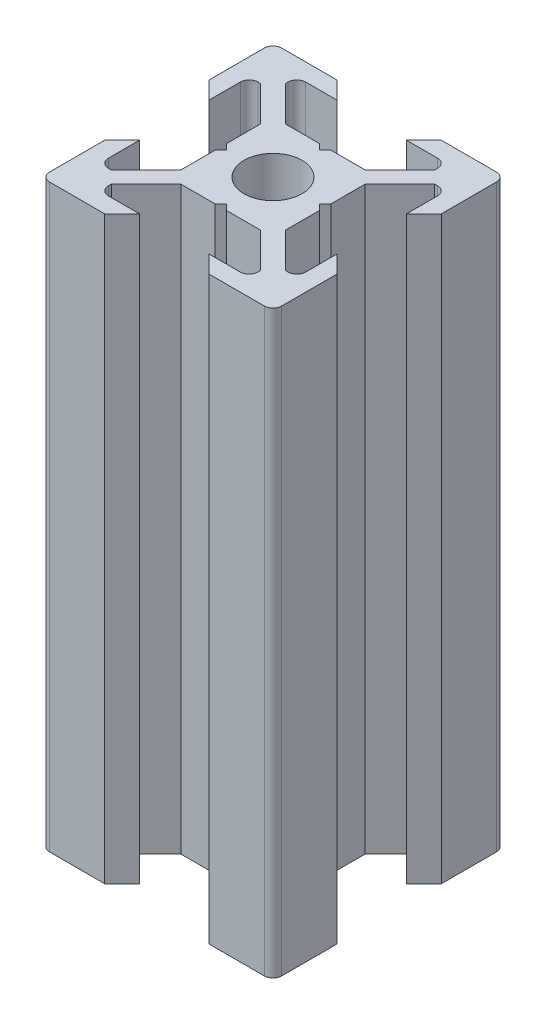
SolidWorks part; units mm, degrees
ref_plane "Face" through (0, 0, 0) normal (0, 0, 1) x (1, 0, 0)
ref_plane "Dessus" through (0, 0, 0) normal (0, 1, 0) x (1, 0, 0)
ref_plane "Droite" through (0, 0, 0) normal (1, 0, 0) x (0, 0, -1)
sketch "Esquisse1" plane through (0, 0, 0) normal (0, 1, 0) x (1, 0, 0)
  line L0 (0, 0) -> (0, 10) construction
  line L1 (0, 0) -> (-10, 0) construction
  line L2 (-10, 0) -> (-10, 10) construction
  line L3 (-10, 10) -> (0, 10) construction
  line L4 (0, 4) -> (-0.5, 4.5)
  line L5 (-0.5, 4.5) -> (-3.4393, 4.5)
  line L6 (-3.4393, 4.5) -> (-6.4393, 7.5)
  line L7 (-6.4393, 7.5) -> (-6.4393, 8.5)
  line L8 (-6.4393, 8.5) -> (-3, 8.5)
  line L9 (-3, 8.5) -> (-4.5, 10)
  line L10 (-4.5, 10) -> (-10, 10)
  line L11 (0, 0) -> (-10, 10) construction
  line L12 (-10, 4.5) -> (-10, 10)
  line L13 (-8.5, 3) -> (-10, 4.5)
  line L14 (-8.5, 6.4393) -> (-8.5, 3)
  line L15 (-7.5, 6.4393) -> (-8.5, 6.4393)
  line L16 (-4.5, 3.4393) -> (-7.5, 6.4393)
  line L17 (-4.5, 0.5) -> (-4.5, 3.4393)
  line L18 (-4, 0) -> (-4.5, 0.5)
  line L19 (0, -4) -> (-0.5, -4.5)
  line L20 (-0.5, -4.5) -> (-3.4393, -4.5)
  line L21 (-4, 0) -> (-4.5, -0.5)
  line L22 (-4.5, -0.5) -> (-4.5, -3.4393)
  line L23 (-4.5, -3.4393) -> (-7.5, -6.4393)
  line L24 (-3.4393, -4.5) -> (-6.4393, -7.5)
  line L25 (-3, -8.5) -> (-4.5, -10)
  line L26 (-6.4393, -8.5) -> (-3, -8.5)
  line L27 (-6.4393, -7.5) -> (-6.4393, -8.5)
  line L28 (-7.5, -6.4393) -> (-8.5, -6.4393)
  line L29 (-4.5, -10) -> (-10, -10)
  line L30 (-10, -4.5) -> (-10, -10)
  line L31 (-8.5, -3) -> (-10, -4.5)
  line L32 (-8.5, -6.4393) -> (-8.5, -3)
  line L33 (8.5, -6.4393) -> (8.5, -3)
  line L34 (8.5, -3) -> (10, -4.5)
  line L35 (10, -4.5) -> (10, -10)
  line L36 (4.5, -10) -> (10, -10)
  line L37 (7.5, -6.4393) -> (8.5, -6.4393)
  line L38 (6.4393, -7.5) -> (6.4393, -8.5)
  line L39 (6.4393, -8.5) -> (3, -8.5)
  line L40 (3, -8.5) -> (4.5, -10)
  line L41 (3.4393, -4.5) -> (6.4393, -7.5)
  line L42 (4.5, -3.4393) -> (7.5, -6.4393)
  line L43 (4.5, -0.5) -> (4.5, -3.4393)
  line L44 (4, 0) -> (4.5, -0.5)
  line L45 (0.5, -4.5) -> (3.4393, -4.5)
  line L46 (0, -4) -> (0.5, -4.5)
  line L47 (4, 0) -> (4.5, 0.5)
  line L48 (4.5, 0.5) -> (4.5, 3.4393)
  line L49 (4.5, 3.4393) -> (7.5, 6.4393)
  line L50 (7.5, 6.4393) -> (8.5, 6.4393)
  line L51 (8.5, 6.4393) -> (8.5, 3)
  line L52 (8.5, 3) -> (10, 4.5)
  line L53 (10, 4.5) -> (10, 10)
  line L54 (4.5, 10) -> (10, 10)
  line L55 (3, 8.5) -> (4.5, 10)
  line L56 (6.4393, 8.5) -> (3, 8.5)
  line L57 (6.4393, 7.5) -> (6.4393, 8.5)
  line L58 (3.4393, 4.5) -> (6.4393, 7.5)
  line L59 (0.5, 4.5) -> (3.4393, 4.5)
  line L60 (0, 4) -> (0.5, 4.5)
  circle A0 centre (0, 0) radius 2.5
  dimension "D10" = 5
  dimension "D1" = 10
  dimension "D2" = 45
  dimension "D3" = 45
  dimension "D4" = 1.5
  dimension "D5" = 7
  dimension "D6" = 1
  dimension "D7" = 4.5
  dimension "D8" = 0.5
  dimension "D9" = 0.75
extrude "Extrusion1" add sketch "Esquisse1" along normal blind 50
fillet "Congé1" radius 0.75 12 edges at (-8.5, 25, -6.4393) (-6.4393, 25, -8.5) (8.5, 25, -6.4393) (6.4393, 25, -8.5) (-8.5, 25, 6.4393) (-6.4393, 25, 8.5) (8.5, 25, 6.4393) (6.4393, 25, 8.5) (10, 25, -10) (-10, 25, -10) (-10, 25, 10) (10, 25, 10)
